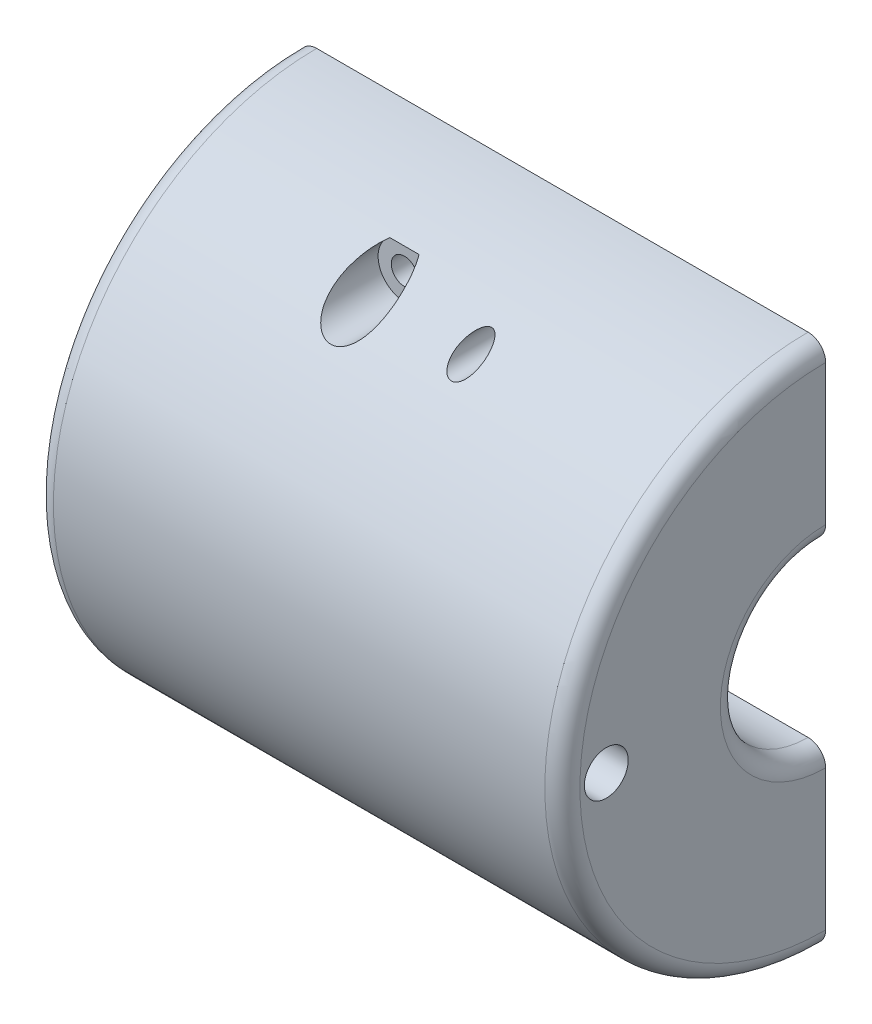
SolidWorks part; units mm, degrees
ref_plane "Front Plane" through (0, 0, 0) normal (0, 0, 1) x (1, 0, 0)
ref_plane "Top Plane" through (0, 0, 0) normal (0, 1, 0) x (1, 0, 0)
ref_plane "Right Plane" through (0, 0, 0) normal (1, 0, 0) x (0, 0, -1)
sketch "Sketch1" plane through (0, 0, 0) normal (1, 0, 0) x (0, 0, -1)
  circle A0 centre (0, 0) radius 38.1
  dimension "D1" = 76.2
extrude "Boss-Extrude1" add sketch "Sketch1" along normal blind 25.4
sketch "Sketch2" plane through (25.4, 0, 0) normal (1, 0, 0) x (0, 0, -1)
  circle A0 centre (0, 0) radius 38.1
  circle A1 centre (0, 0) radius 25.4
  circle A2 centre (0, 0) radius 38.1 construction
  dimension "D1" = 50.8
extrude "Boss-Extrude2" add sketch "Sketch2" along normal blind 25.4
sketch "Sketch3" plane through (50.8, 0, 0) normal (1, 0, 0) x (0, 0, -1)
  circle A0 centre (0, 0) radius 38.1
extrude "Boss-Extrude3" add sketch "Sketch3" along normal blind 25.4
sketch "Sketch4" plane through (76.2, 0, 0) normal (1, 0, 0) x (0, 0, -1)
  circle A0 centre (0, 0) radius 12.7
  dimension "D1" = 25.4
extrude "Cut-Extrude1" cut sketch "Sketch4" against normal through all
fillet "Fillet1" radius 2.54 2 edges at (0, 0, -38.1) (76.2, 0, -38.1)
sketch "Sketch6" plane through (0, 0, 0) normal (0, 0, 1) x (1, 0, 0)
  line L0 (45.72, -31.75) -> (45.72, 31.75) construction
  line L1 (45.72, 31.75) -> (30.48, 31.75) construction
  line L2 (30.48, 31.75) -> (30.48, -31.75) construction
  line L3 (38.1, 31.75) -> (38.1, 38.1) construction
  line L4 (73.66, 38.1) -> (2.54, 38.1) construction
  line L5 (38.1, -25.4) -> (38.1, 31.75) construction
  line L6 (25.4, -25.4) -> (50.8, -25.4) construction
  line L7 (0, 0) -> (45.72, 0) construction
  line L8 (38.1, 31.75) -> (38.1, 25.4) construction
  line L9 (50.8, 25.4) -> (25.4, 25.4) construction
  circle A0 centre (30.48, 31.75) radius 1.905
  circle A1 centre (45.72, 31.75) radius 1.905
  circle A2 centre (30.48, -31.75) radius 1.905
  circle A3 centre (45.72, -31.75) radius 1.905
  dimension "D2" = 3.81
  dimension "D1" = 15.24
extrude "Cut-Extrude2" cut sketch "Sketch6" against normal through all both and the other way through all
ref_plane "Plane1" through (0, 0, 15.24) normal (0, 0, 1) x (1, 0, 0)
sketch "Sketch7" plane through (0, 0, 15.24) normal (0, 0, 1) x (1, 0, 0)
  circle A0 centre (30.48, 31.75) radius 3.81
  circle A1 centre (45.72, -31.75) radius 3.81
  dimension "D1" = 7.62
extrude "Cut-Extrude3" cut sketch "Sketch7" along normal blind 25.4
ref_plane "Plane2" through (0, 0, -15.24) normal (0, 0, 1) x (1, 0, 0)
sketch "Sketch8" plane through (0, 0, -15.24) normal (0, 0, 1) x (1, 0, 0)
  circle A0 centre (45.72, 31.75) radius 3.81
  circle A1 centre (30.48, -31.75) radius 3.81
  arc A2 (28.3653, 34.9192) -> (32.5947, 34.9192) centre (30.48, 31.75) ccw construction
  circle A3 centre (45.72, 31.75) radius 1.905 construction
extrude "Cut-Extrude4" cut sketch "Sketch8" against normal blind 25.4
sketch "Sketch9" plane through (0, 0, 0) normal (-1, 0, 0) x (0, 0, 1)
  line L1 (0, 38.1) -> (-50.8, 38.1)
  line L2 (0, 38.1) -> (0, -38.1)
  line L3 (0, -38.1) -> (-50.8, -38.1)
  line L4 (-50.8, 38.1) -> (-50.8, -38.1)
  circle A0 centre (0, 0) radius 38.1 construction
  dimension "D1" = 50.8
extrude "Cut-Extrude5" cut sketch "Sketch9" against normal up to next
fillet "Fillet2" radius 2.54 2 edges at (25.4, 0, 12.7) (50.8, 0, 12.7)
sketch "Sketch10" plane through (76.2, 0, 0) normal (1, 0, 0) x (0, 0, -1)
  circle A0 centre (0, 0) radius 31.75 construction
  circle A1 centre (-31.75, 0) radius 3.175
  dimension "D1" = 63.5
  dimension "D2" = 6.35
extrude "Cut-Extrude6" cut sketch "Sketch10" against normal through all
fillet "Fillet3" radius 2.54 2 edges at (0, 0, 12.7) (76.2, 0, 12.7)
